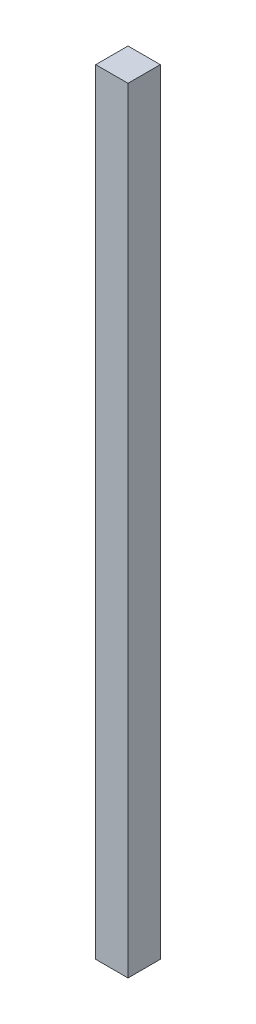
SolidWorks part; units mm, degrees
ref_plane "Front Plane" through (0, 0, 0) normal (0, 0, 1) x (1, 0, 0)
ref_plane "Top Plane" through (0, 0, 0) normal (0, 1, 0) x (1, 0, 0)
ref_plane "Right Plane" through (0, 0, 0) normal (1, 0, 0) x (0, 0, -1)
sketch "Sketch1" plane through (0, 0, 0) normal (0, 1, 0) x (1, 0, 0)
  line L0 (0, 12.7) -> (0, 0) construction
  line L1 (0, 0) -> (12.7, 0) construction
  line L2 (-12.7, 12.7) -> (12.7, 12.7)
  line L3 (12.7, 12.7) -> (12.7, -12.7)
  line L4 (-12.7, 12.7) -> (-12.7, -12.7)
  line L5 (-12.7, -12.7) -> (12.7, -12.7)
  point P8 (-12.7, 0)
  dimension "D1" = 25.4
extrude "Boss-Extrude1" add sketch "Sketch1" along normal mid plane 609.6
